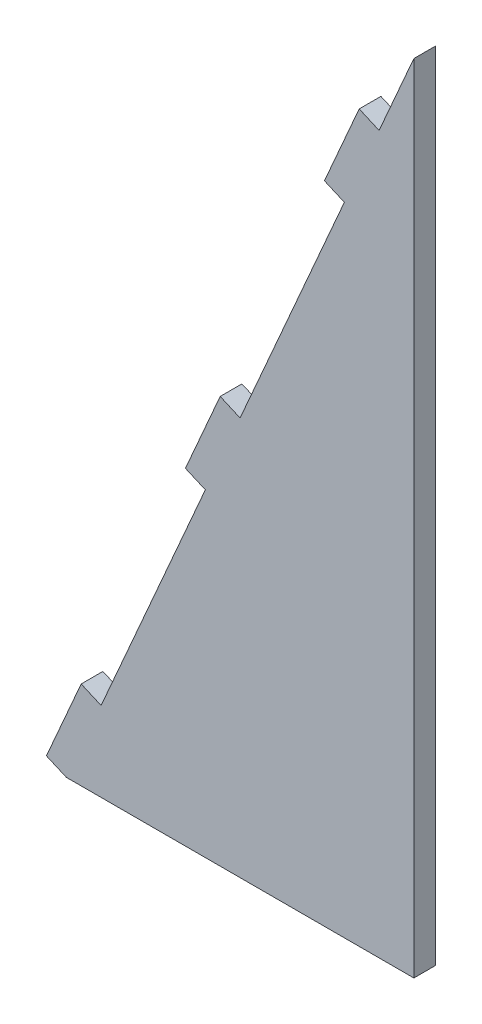
SolidWorks part; units mm, degrees
ref_plane "Front Plane" through (0, 0, 0) normal (0, 0, 1) x (1, 0, 0)
ref_plane "Top Plane" through (0, 0, 0) normal (0, 1, 0) x (1, 0, 0)
ref_plane "Right Plane" through (0, 0, 0) normal (1, 0, 0) x (0, 0, -1)
sketch "Sketch1" plane through (0, 0, 0) normal (0, 0, 1) x (1, 0, 0)
  line L0 (0, 0) -> (50.8, 0)
  line L1 (50.8, 0) -> (50.8, 116.3974)
  line L2 (50.8, 116.3974) -> (0, 0)
  dimension "D1" = 50.8
  dimension "D2" = 127
extrude "Extrude1" add sketch "Sketch1" along normal blind 3.175
sketch "Sketch2" plane through (0, 0, 0) normal (-0.9165, 0.4, 0) x (0, 0, 1)
  line L0 (3.175, 127) -> (3.175, 0) construction
  line L1 (0, 0) -> (3.175, 0)
  line L2 (0, 0) -> (0, 12.7)
  line L3 (0, 12.7) -> (3.175, 12.7)
  line L4 (3.175, 0) -> (3.175, 12.7)
  dimension "D1" = 12.7
  dimension "D2" = 3.175
extrude "Extrude2" add sketch "Sketch2" along normal blind 3.175
pattern_linear "LPattern1" count 3 spacing 50.8 along (0.4, 0.9165, 0) of "Extrude2"
